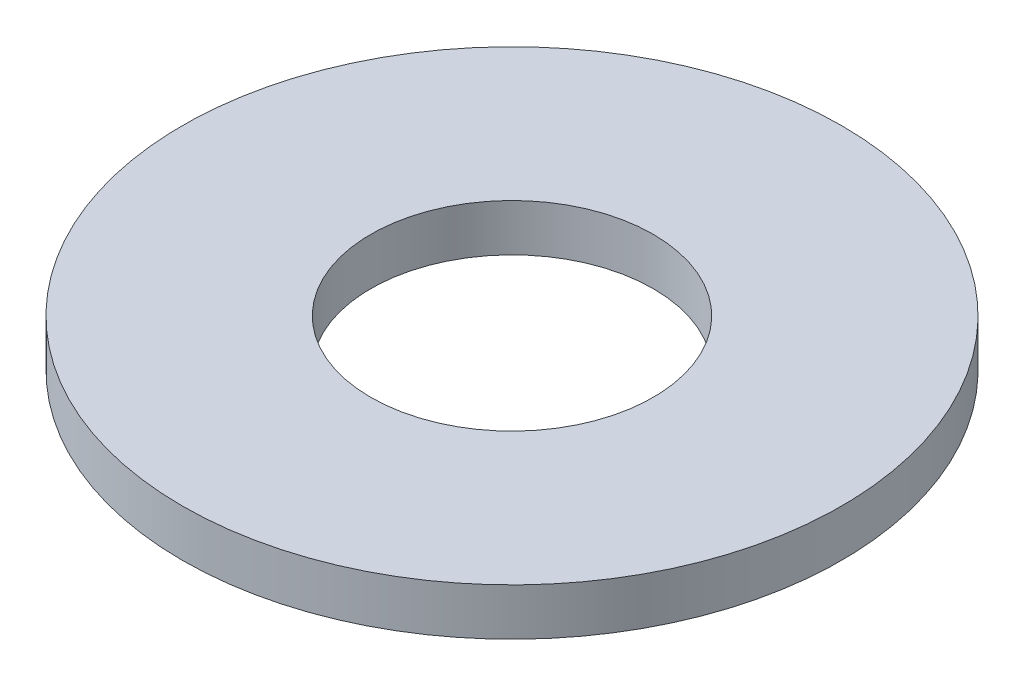
SolidWorks part; units mm, degrees
material "AISI 304"
ref_plane "前视基准面" through (0, 0, 0) normal (0, 0, 1) x (1, 0, 0)
ref_plane "上视基准面" through (0, 0, 0) normal (0, 1, 0) x (1, 0, 0)
ref_plane "右视基准面" through (0, 0, 0) normal (1, 0, 0) x (0, 0, -1)
sketch "草图1" plane through (0, 0, 0) normal (0, 1, 0) x (1, 0, 0)
  circle A0 centre (0, 0) radius 1.5
  circle A1 centre (0, 0) radius 3.5
  dimension "内径" = 3
  dimension "外径" = 7
extrude "凸台-拉伸1" add sketch "草图1" along normal blind 0.5
